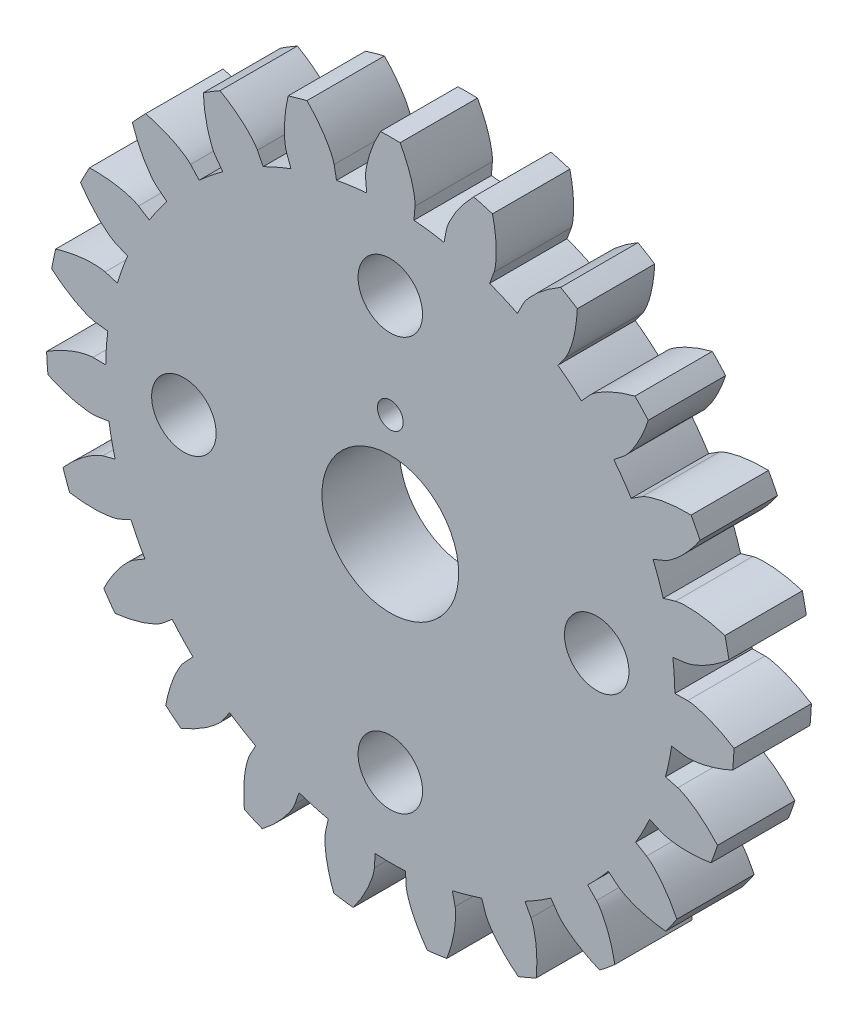
SolidWorks part; units mm, degrees
ref_plane "Front Plane" through (0, 0, 0) normal (0, 0, 1) x (1, 0, 0)
ref_plane "Top Plane" through (0, 0, 0) normal (0, 1, 0) x (1, 0, 0)
ref_plane "Right Plane" through (0, 0, 0) normal (1, 0, 0) x (0, 0, -1)
sketch "Model" plane through (0, 0, 0) normal (0, 0, 1) x (1, 0, 0)
  line L0 (-3.5387, -10.448) -> (-3.6973, -10.9162)
  line L1 (-5.4543, -10.153) -> (-5.2204, -9.7176)
  line L2 (-6.2264, -9.1058) -> (-6.5054, -9.5139)
  line L3 (-7.9913, -8.3049) -> (-7.6486, -7.9488)
  line L4 (-8.4522, -7.0883) -> (-8.8309, -7.4059)
  line L5 (-9.9356, -5.8409) -> (-9.5095, -5.5904)
  line L6 (-10.0512, -4.5451) -> (-10.5016, -4.7487)
  line L7 (-11.1431, -2.9437) -> (-10.6651, -2.8175)
  line L8 (-10.9047, -1.6648) -> (-11.3933, -1.7394)
  line L9 (-11.524, 0.1718) -> (-11.0298, 0.1644)
  line L10 (-10.9495, 1.339) -> (-11.4401, 1.399)
  line L11 (-11.0504, 3.2746) -> (-10.5764, 3.1341)
  line L12 (-10.1822, 4.2435) -> (-10.6384, 4.4336)
  line L13 (-9.7571, 6.1345) -> (-9.3387, 5.8714)
  line L14 (-8.6597, 6.8332) -> (-9.0477, 7.1394)
  line L15 (-7.7402, 8.5394) -> (-7.4083, 8.1732)
  line L16 (-6.495, 8.9162) -> (-6.786, 9.3157)
  line L17 (-5.1493, 10.3111) -> (-4.9285, 9.8688)
  line L18 (-3.8486, 10.3379) -> (-4.021, 10.8011)
  line L19 (-2.1765, 11.318) -> (-2.0831, 10.8326)
  line L20 (-0.9167, 10.9929) -> (-0.9578, 11.4855)
  line L21 (0.9578, 11.4855) -> (0.9167, 10.9929)
  line L22 (2.0831, 10.8326) -> (2.1765, 11.318)
  line L23 (4.021, 10.8011) -> (3.8486, 10.3379)
  line L24 (4.9285, 9.8688) -> (5.1493, 10.3111)
  line L25 (6.786, 9.3157) -> (6.495, 8.9162)
  line L26 (7.4083, 8.1732) -> (7.7402, 8.5394)
  line L27 (9.0477, 7.1394) -> (8.6597, 6.8332)
  line L28 (9.3387, 5.8714) -> (9.7571, 6.1345)
  line L29 (10.6384, 4.4336) -> (10.1822, 4.2435)
  line L30 (10.5764, 3.1341) -> (11.0504, 3.2746)
  line L31 (11.4401, 1.399) -> (10.9495, 1.339)
  line L32 (11.0298, 0.1644) -> (11.524, 0.1718)
  line L33 (11.3933, -1.7394) -> (10.9047, -1.6648)
  line L34 (10.6651, -2.8175) -> (11.1431, -2.9437)
  line L35 (10.5016, -4.7487) -> (10.0512, -4.5451)
  line L36 (9.5095, -5.5904) -> (9.9356, -5.8409)
  line L37 (8.8309, -7.4059) -> (8.4522, -7.0883)
  line L38 (7.6486, -7.9488) -> (7.9913, -8.3049)
  line L39 (6.5054, -9.5139) -> (6.2264, -9.1058)
  line L40 (5.2204, -9.7176) -> (5.4543, -10.153)
  line L41 (3.6973, -10.9162) -> (3.5387, -10.448)
  line L42 (2.405, -10.7657) -> (2.5128, -11.2481)
  line L43 (0.6151, -11.5089) -> (0.5887, -11.0153)
  line L44 (-0.5887, -11.0153) -> (-0.6151, -11.5089)
  line L45 (-2.5128, -11.2481) -> (-2.405, -10.7657)
  arc A0 (-5.6568, -12.0719) -> (-4.9615, -12.3739) centre (0, 0) ccw
  arc A1 (-6.2264, -9.1058) -> (-5.2204, -9.7176) centre (0, 0) ccw
  arc A2 (-8.704, -10.098) -> (-8.1159, -10.5765) centre (0, 0) ccw
  arc A3 (-8.4522, -7.0883) -> (-7.6486, -7.9488) centre (0, 0) ccw
  arc A4 (-11.1057, -7.3752) -> (-10.6684, -7.9946) centre (0, 0) ccw
  arc A5 (-10.0512, -4.5451) -> (-9.5095, -5.5904) centre (0, 0) ccw
  arc A6 (-12.6836, -4.1055) -> (-12.4297, -4.8198) centre (0, 0) ccw
  arc A7 (-10.9047, -1.6648) -> (-10.6651, -2.8175) centre (0, 0) ccw
  arc A8 (-13.3209, -0.5312) -> (-13.2692, -1.2876) centre (0, 0) ccw
  arc A9 (-10.9495, 1.339) -> (-11.0298, 0.1644) centre (0, 0) ccw
  arc A10 (-12.9703, 3.0824) -> (-13.1245, 2.3401) centre (0, 0) ccw
  arc A11 (-10.1822, 4.2435) -> (-10.5764, 3.1341) centre (0, 0) ccw
  arc A12 (-11.6577, 6.4675) -> (-12.0065, 5.7943) centre (0, 0) ccw
  arc A13 (-8.6597, 6.8332) -> (-9.3387, 5.8714) centre (0, 0) ccw
  arc A14 (-9.4805, 9.3728) -> (-9.998, 8.8187) centre (0, 0) ccw
  arc A15 (-6.495, 8.9162) -> (-7.4083, 8.1732) centre (0, 0) ccw
  arc A16 (-6.6002, 11.5831) -> (-7.2479, 11.1891) centre (0, 0) ccw
  arc A17 (-3.8486, 10.3379) -> (-4.9285, 9.8688) centre (0, 0) ccw
  arc A18 (-3.2303, 12.9342) -> (-3.9604, 12.7297) centre (0, 0) ccw
  arc A19 (-0.9167, 10.9929) -> (-2.0831, 10.8326) centre (0, 0) ccw
  arc A20 (0.3791, 13.3261) -> (-0.3791, 13.3261) centre (0, 0) ccw
  arc A21 (2.0831, 10.8326) -> (0.9167, 10.9929) centre (0, 0) ccw
  arc A22 (3.9604, 12.7297) -> (3.2303, 12.9342) centre (0, 0) ccw
  arc A23 (4.9285, 9.8688) -> (3.8486, 10.3379) centre (0, 0) ccw
  arc A24 (7.2479, 11.1891) -> (6.6002, 11.5831) centre (0, 0) ccw
  arc A25 (7.4083, 8.1732) -> (6.495, 8.9162) centre (0, 0) ccw
  arc A26 (9.998, 8.8187) -> (9.4805, 9.3728) centre (0, 0) ccw
  arc A27 (9.3387, 5.8714) -> (8.6597, 6.8332) centre (0, 0) ccw
  arc A28 (12.0065, 5.7943) -> (11.6577, 6.4675) centre (0, 0) ccw
  arc A29 (10.5764, 3.1341) -> (10.1822, 4.2435) centre (0, 0) ccw
  arc A30 (13.1245, 2.3401) -> (12.9703, 3.0824) centre (0, 0) ccw
  arc A31 (11.0298, 0.1644) -> (10.9495, 1.339) centre (0, 0) ccw
  arc A32 (13.2692, -1.2876) -> (13.3209, -0.5312) centre (0, 0) ccw
  arc A33 (10.6651, -2.8175) -> (10.9047, -1.6648) centre (0, 0) ccw
  arc A34 (12.4297, -4.8198) -> (12.6836, -4.1055) centre (0, 0) ccw
  arc A35 (9.5095, -5.5904) -> (10.0512, -4.5451) centre (0, 0) ccw
  arc A36 (10.6684, -7.9946) -> (11.1057, -7.3752) centre (0, 0) ccw
  arc A37 (7.6486, -7.9488) -> (8.4522, -7.0883) centre (0, 0) ccw
  arc A38 (8.1159, -10.5765) -> (8.704, -10.098) centre (0, 0) ccw
  arc A39 (5.2204, -9.7176) -> (6.2264, -9.1058) centre (0, 0) ccw
  arc A40 (4.9615, -12.3739) -> (5.6568, -12.0719) centre (0, 0) ccw
  arc A41 (2.405, -10.7657) -> (3.5387, -10.448) centre (0, 0) ccw
  arc A42 (1.439, -13.2536) -> (2.1901, -13.1504) centre (0, 0) ccw
  arc A43 (-0.5887, -11.0153) -> (0.5887, -11.0153) centre (0, 0) ccw
  arc A44 (-2.1901, -13.1504) -> (-1.439, -13.2536) centre (0, 0) ccw
  arc A45 (-3.5387, -10.448) -> (-2.405, -10.7657) centre (0, 0) ccw
  circle A46 centre (0, 0) radius 12.265 construction
  spline S0 degree 3 poles (-3.6973, -10.9162) (-3.7069, -10.9403) (-3.7475, -11.036) (-3.8652, -11.2386) (-4.0935, -11.5548) (-4.4634, -11.9567) (-4.7761, -12.2317) (-4.9615, -12.3739) knots 34.584629 34.584629 34.584629 34.584629 34.662509 34.896108 35.285436 35.830493 36.531279 36.531279 36.531279 36.531279
  spline S1 degree 3 poles (-5.6568, -12.0719) (-5.6795, -11.8394) (-5.6919, -11.4231) (-5.6506, -10.8784) (-5.5754, -10.4958) (-5.5076, -10.2714) (-5.4654, -10.1765) (-5.4543, -10.153) knots 37.289537 37.289537 37.289537 37.289537 37.990323 38.535379 38.924707 39.158307 39.236186 39.236186 39.236186 39.236186
  spline S2 degree 3 poles (-6.5054, -9.5139) (-6.5211, -9.5345) (-6.586, -9.6157) (-6.754, -9.779) (-7.0591, -10.0219) (-7.5237, -10.3091) (-7.8991, -10.4896) (-8.1159, -10.5765) knots 41.402696 41.402696 41.402696 41.402696 41.480575 41.714175 42.103503 42.648559 43.349345 43.349345 43.349345 43.349345
  spline S3 degree 3 poles (-8.704, -10.098) (-8.6631, -9.868) (-8.5627, -9.4638) (-8.376, -8.9505) (-8.2003, -8.6023) (-8.0746, -8.4046) (-8.0083, -8.3246) (-7.9913, -8.3049) knots 44.107603 44.107603 44.107603 44.107603 44.808389 45.353446 45.742774 45.976373 46.054253 46.054253 46.054253 46.054253
  spline S4 degree 3 poles (-8.8309, -7.4059) (-8.8517, -7.4216) (-8.936, -7.4822) (-9.1419, -7.5942) (-9.5012, -7.7457) (-10.0261, -7.8969) (-10.4362, -7.9695) (-10.6684, -7.9946) knots 48.220763 48.220763 48.220763 48.220763 48.298642 48.532242 48.921569 49.466626 50.167412 50.167412 50.167412 50.167412
  spline S5 degree 3 poles (-11.1057, -7.3752) (-11.0042, -7.1648) (-10.7985, -6.8027) (-10.4802, -6.3587) (-10.2171, -6.0709) (-10.0427, -5.9144) (-9.9573, -5.8552) (-9.9356, -5.8409) knots 50.92567 50.92567 50.92567 50.92567 51.626456 52.171513 52.56084 52.79444 52.87232 52.87232 52.87232 52.87232
  spline S6 degree 3 poles (-10.5016, -4.7487) (-10.5257, -4.7582) (-10.6233, -4.7938) (-10.8518, -4.8461) (-11.2386, -4.8951) (-11.7849, -4.8991) (-12.1993, -4.8583) (-12.4297, -4.8198) knots 55.038829 55.038829 55.038829 55.038829 55.116709 55.350309 55.739636 56.284693 56.985479 56.985479 56.985479 56.985479
  spline S7 degree 3 poles (-12.6836, -4.1055) (-12.5292, -3.9302) (-12.2334, -3.637) (-11.8072, -3.2954) (-11.4762, -3.0892) (-11.266, -2.9856) (-11.1678, -2.9517) (-11.1431, -2.9437) knots 57.743737 57.743737 57.743737 57.743737 58.444523 58.98958 59.378907 59.612507 59.690386 59.690386 59.690386 59.690386
  spline S8 degree 3 poles (-11.3933, -1.7394) (-11.4192, -1.7419) (-11.5228, -1.7499) (-11.7568, -1.7386) (-12.1426, -1.6814) (-12.6696, -1.5379) (-13.0577, -1.3868) (-13.2692, -1.2876) knots 61.856896 61.856896 61.856896 61.856896 61.934776 62.168375 62.557703 63.102759 63.803546 63.803546 63.803546 63.803546
  spline S9 degree 3 poles (-13.3209, -0.5312) (-13.1249, -0.4042) (-12.761, -0.2016) (-12.2584, 0.0123) (-11.8841, 0.1216) (-11.6537, 0.1646) (-11.55, 0.1708) (-11.524, 0.1718) knots 64.561804 64.561804 64.561804 64.561804 65.26259 65.807646 66.196974 66.430574 66.508453 66.508453 66.508453 66.508453
  spline S10 degree 3 poles (-11.4401, 1.399) (-11.4657, 1.4035) (-11.5676, 1.4238) (-11.7899, 1.4978) (-12.1459, 1.657) (-12.6147, 1.9374) (-12.9476, 2.1876) (-13.1245, 2.3401) knots 68.674963 68.674963 68.674963 68.674963 68.752842 68.986442 69.37577 69.920826 70.621612 70.621612 70.621612 70.621612
  spline S11 degree 3 poles (-12.9703, 3.0824) (-12.7472, 3.1519) (-12.3422, 3.2487) (-11.8005, 3.3192) (-11.4106, 3.3233) (-11.1772, 3.3026) (-11.0756, 3.2806) (-11.0504, 3.2746) knots 71.37987 71.37987 71.37987 71.37987 72.080656 72.625713 73.015041 73.24864 73.32652 73.32652 73.32652 73.32652
  spline S12 degree 3 poles (-10.6384, 4.4336) (-10.6618, 4.4449) (-10.7545, 4.4919) (-10.9486, 4.6231) (-11.2485, 4.8724) (-11.6242, 5.2689) (-11.8773, 5.5997) (-12.0065, 5.7943) knots 75.493029 75.493029 75.493029 75.493029 75.570909 75.804509 76.193836 76.738893 77.439679 77.439679 77.439679 77.439679
  spline S13 degree 3 poles (-11.6577, 6.4675) (-11.4242, 6.4742) (-11.008, 6.4581) (-10.4674, 6.3798) (-10.0908, 6.2786) (-9.8716, 6.1957) (-9.7798, 6.1471) (-9.7571, 6.1345) knots 78.197937 78.197937 78.197937 78.197937 78.898723 79.44378 79.833107 80.066707 80.144586 80.144586 80.144586 80.144586
  spline S14 degree 3 poles (-9.0477, 7.1394) (-9.0673, 7.1566) (-9.1438, 7.2268) (-9.2953, 7.4056) (-9.5168, 7.7266) (-9.7716, 8.2097) (-9.9261, 8.5965) (-9.998, 8.8187) knots 82.311096 82.311096 82.311096 82.311096 82.388976 82.622575 83.011903 83.55696 84.257746 84.257746 84.257746 84.257746
  spline S15 degree 3 poles (-9.4805, 9.3728) (-9.2538, 9.3163) (-8.8574, 9.1886) (-8.358, 8.9673) (-8.0227, 8.7683) (-7.834, 8.6293) (-7.7586, 8.5577) (-7.7402, 8.5394) knots 85.016004 85.016004 85.016004 85.016004 85.71679 86.261846 86.651174 86.884774 86.962653 86.962653 86.962653 86.962653
  spline S16 degree 3 poles (-6.786, 9.3157) (-6.8002, 9.3375) (-6.8549, 9.4258) (-6.9526, 9.6388) (-7.0793, 10.0076) (-7.1943, 10.5416) (-7.2387, 10.9557) (-7.2479, 11.1891) knots 89.129163 89.129163 89.129163 89.129163 89.207042 89.440642 89.82997 90.375026 91.075812 91.075812 91.075812 91.075812
  spline S17 degree 3 poles (-6.6002, 11.5831) (-6.3972, 11.4675) (-6.0499, 11.2375) (-5.6287, 10.8897) (-5.3595, 10.6076) (-5.2153, 10.4229) (-5.1621, 10.3337) (-5.1493, 10.3111) knots 91.83407 91.83407 91.83407 91.83407 92.534856 93.079913 93.469241 93.70284 93.78072 93.78072 93.78072 93.78072
  spline S18 degree 3 poles (-4.021, 10.8011) (-4.0288, 10.8259) (-4.0577, 10.9257) (-4.0943, 11.1572) (-4.1167, 11.5465) (-4.0834, 12.0917) (-4.0144, 12.5024) (-3.9604, 12.7297) knots 95.947229 95.947229 95.947229 95.947229 96.025109 96.258709 96.648036 97.193093 97.893879 97.893879 97.893879 97.893879
  spline S19 degree 3 poles (-3.2303, 12.9342) (-3.0661, 12.7682) (-2.7937, 12.4531) (-2.482, 12.0045) (-2.2989, 11.6602) (-2.2099, 11.4435) (-2.1827, 11.3432) (-2.1765, 11.318) knots 98.652137 98.652137 98.652137 98.652137 99.352923 99.89798 100.287307 100.520907 100.598787 100.598787 100.598787 100.598787
  spline S20 degree 3 poles (-0.9578, 11.4855) (-0.9586, 11.5114) (-0.9595, 11.6153) (-0.9323, 11.8481) (-0.8489, 12.229) (-0.6697, 12.745) (-0.4925, 13.1219) (-0.3791, 13.3261) knots 102.765296 102.765296 102.765296 102.765296 102.843176 103.076775 103.466103 104.01116 104.711946 104.711946 104.711946 104.711946
  spline S21 degree 3 poles (0.3791, 13.3261) (0.4925, 13.1219) (0.6697, 12.745) (0.8489, 12.229) (0.9323, 11.8481) (0.9595, 11.6153) (0.9586, 11.5114) (0.9578, 11.4855) knots 105.470204 105.470204 105.470204 105.470204 106.17099 106.716046 107.105374 107.338974 107.416853 107.416853 107.416853 107.416853
  spline S22 degree 3 poles (2.1765, 11.318) (2.1827, 11.3432) (2.2099, 11.4435) (2.2989, 11.6602) (2.482, 12.0045) (2.7937, 12.4531) (3.0661, 12.7682) (3.2303, 12.9342) knots 109.583363 109.583363 109.583363 109.583363 109.661242 109.894842 110.28417 110.829226 111.530012 111.530012 111.530012 111.530012
  spline S23 degree 3 poles (3.9604, 12.7297) (4.0144, 12.5024) (4.0834, 12.0917) (4.1167, 11.5465) (4.0943, 11.1572) (4.0577, 10.9257) (4.0288, 10.8259) (4.021, 10.8011) knots 112.28827 112.28827 112.28827 112.28827 112.989057 113.534113 113.923441 114.15704 114.23492 114.23492 114.23492 114.23492
  spline S24 degree 3 poles (5.1493, 10.3111) (5.1621, 10.3337) (5.2153, 10.4229) (5.3595, 10.6076) (5.6287, 10.8897) (6.0499, 11.2375) (6.3972, 11.4675) (6.6002, 11.5831) knots 116.40143 116.40143 116.40143 116.40143 116.479309 116.712909 117.102236 117.647293 118.348079 118.348079 118.348079 118.348079
  spline S25 degree 3 poles (7.2479, 11.1891) (7.2387, 10.9557) (7.1943, 10.5416) (7.0793, 10.0076) (6.9526, 9.6388) (6.8549, 9.4258) (6.8002, 9.3375) (6.786, 9.3157) knots 119.106337 119.106337 119.106337 119.106337 119.807123 120.35218 120.741507 120.975107 121.052987 121.052987 121.052987 121.052987
  spline S26 degree 3 poles (7.7402, 8.5394) (7.7586, 8.5577) (7.834, 8.6293) (8.0227, 8.7683) (8.358, 8.9673) (8.8574, 9.1886) (9.2538, 9.3163) (9.4805, 9.3728) knots 123.219496 123.219496 123.219496 123.219496 123.297376 123.530976 123.920303 124.46536 125.166146 125.166146 125.166146 125.166146
  spline S27 degree 3 poles (9.998, 8.8187) (9.9261, 8.5965) (9.7716, 8.2097) (9.5168, 7.7266) (9.2953, 7.4056) (9.1438, 7.2268) (9.0673, 7.1566) (9.0477, 7.1394) knots 125.924404 125.924404 125.924404 125.924404 126.62519 127.170247 127.559574 127.793174 127.871053 127.871053 127.871053 127.871053
  spline S28 degree 3 poles (9.7571, 6.1345) (9.7798, 6.1471) (9.8716, 6.1957) (10.0908, 6.2786) (10.4674, 6.3798) (11.008, 6.4581) (11.4242, 6.4742) (11.6577, 6.4675) knots 130.037563 130.037563 130.037563 130.037563 130.115443 130.349042 130.73837 131.283426 131.984213 131.984213 131.984213 131.984213
  spline S29 degree 3 poles (12.0065, 5.7943) (11.8773, 5.5997) (11.6242, 5.2689) (11.2485, 4.8724) (10.9486, 4.6231) (10.7545, 4.4919) (10.6618, 4.4449) (10.6384, 4.4336) knots 132.742471 132.742471 132.742471 132.742471 133.443257 133.988313 134.377641 134.611241 134.68912 134.68912 134.68912 134.68912
  spline S30 degree 3 poles (11.0504, 3.2746) (11.0756, 3.2806) (11.1772, 3.3026) (11.4106, 3.3233) (11.8005, 3.3192) (12.3422, 3.2487) (12.7472, 3.1519) (12.9703, 3.0824) knots 136.85563 136.85563 136.85563 136.85563 136.933509 137.167109 137.556437 138.101493 138.802279 138.802279 138.802279 138.802279
  spline S31 degree 3 poles (13.1245, 2.3401) (12.9476, 2.1876) (12.6147, 1.9374) (12.1459, 1.657) (11.7899, 1.4978) (11.5676, 1.4238) (11.4657, 1.4035) (11.4401, 1.399) knots 139.560537 139.560537 139.560537 139.560537 140.261323 140.80638 141.195708 141.429307 141.507187 141.507187 141.507187 141.507187
  spline S32 degree 3 poles (11.524, 0.1718) (11.55, 0.1708) (11.6537, 0.1646) (11.8841, 0.1216) (12.2584, 0.0123) (12.761, -0.2016) (13.1249, -0.4042) (13.3209, -0.5312) knots 143.673696 143.673696 143.673696 143.673696 143.751576 143.985176 144.374503 144.91956 145.620346 145.620346 145.620346 145.620346
  spline S33 degree 3 poles (13.2692, -1.2876) (13.0577, -1.3868) (12.6696, -1.5379) (12.1426, -1.6814) (11.7568, -1.7386) (11.5228, -1.7499) (11.4192, -1.7419) (11.3933, -1.7394) knots 146.378604 146.378604 146.378604 146.378604 147.07939 147.624447 148.013774 148.247374 148.325254 148.325254 148.325254 148.325254
  spline S34 degree 3 poles (11.1431, -2.9437) (11.1678, -2.9517) (11.266, -2.9856) (11.4762, -3.0892) (11.8072, -3.2954) (12.2334, -3.637) (12.5292, -3.9302) (12.6836, -4.1055) knots 150.491763 150.491763 150.491763 150.491763 150.569643 150.803242 151.19257 151.737627 152.438413 152.438413 152.438413 152.438413
  spline S35 degree 3 poles (12.4297, -4.8198) (12.1993, -4.8583) (11.7849, -4.8991) (11.2386, -4.8951) (10.8518, -4.8461) (10.6233, -4.7938) (10.5257, -4.7582) (10.5016, -4.7487) knots 153.196671 153.196671 153.196671 153.196671 153.897457 154.442513 154.831841 155.065441 155.14332 155.14332 155.14332 155.14332
  spline S36 degree 3 poles (9.9356, -5.8409) (9.9573, -5.8552) (10.0427, -5.9144) (10.2171, -6.0709) (10.4802, -6.3587) (10.7985, -6.8027) (11.0042, -7.1648) (11.1057, -7.3752) knots 157.30983 157.30983 157.30983 157.30983 157.387709 157.621309 158.010637 158.555693 159.256479 159.256479 159.256479 159.256479
  spline S37 degree 3 poles (10.6684, -7.9946) (10.4362, -7.9695) (10.0261, -7.8969) (9.5012, -7.7457) (9.1419, -7.5942) (8.936, -7.4822) (8.8517, -7.4216) (8.8309, -7.4059) knots 160.014737 160.014737 160.014737 160.014737 160.715523 161.26058 161.649908 161.883507 161.961387 161.961387 161.961387 161.961387
  spline S38 degree 3 poles (7.9913, -8.3049) (8.0083, -8.3246) (8.0746, -8.4046) (8.2003, -8.6023) (8.376, -8.9505) (8.5627, -9.4638) (8.6631, -9.868) (8.704, -10.098) knots 164.127897 164.127897 164.127897 164.127897 164.205776 164.439376 164.828703 165.37376 166.074546 166.074546 166.074546 166.074546
  spline S39 degree 3 poles (8.1159, -10.5765) (7.8991, -10.4896) (7.5237, -10.3091) (7.0591, -10.0219) (6.754, -9.779) (6.586, -9.6157) (6.5211, -9.5345) (6.5054, -9.5139) knots 166.832804 166.832804 166.832804 166.832804 167.53359 168.078647 168.467974 168.701574 168.779454 168.779454 168.779454 168.779454
  spline S40 degree 3 poles (5.4543, -10.153) (5.4654, -10.1765) (5.5076, -10.2714) (5.5754, -10.4958) (5.6506, -10.8784) (5.6919, -11.4231) (5.6795, -11.8394) (5.6568, -12.0719) knots 170.945963 170.945963 170.945963 170.945963 171.023843 171.257442 171.64677 172.191827 172.892613 172.892613 172.892613 172.892613
  spline S41 degree 3 poles (4.9615, -12.3739) (4.7761, -12.2317) (4.4634, -11.9567) (4.0935, -11.5548) (3.8652, -11.2386) (3.7475, -11.036) (3.7069, -10.9403) (3.6973, -10.9162) knots 173.650871 173.650871 173.650871 173.650871 174.351657 174.896713 175.286041 175.519641 175.59752 175.59752 175.59752 175.59752
  spline S42 degree 3 poles (2.5128, -11.2481) (2.5172, -11.2737) (2.5322, -11.3765) (2.5369, -11.6108) (2.5061, -11.9995) (2.3989, -12.5351) (2.2746, -12.9326) (2.1901, -13.1504) knots 177.76403 177.76403 177.76403 177.76403 177.841909 178.075509 178.464837 179.009893 179.710679 179.710679 179.710679 179.710679
  spline S43 degree 3 poles (1.439, -13.2536) (1.2989, -13.0667) (1.072, -12.7175) (0.8242, -12.2307) (0.6897, -11.8647) (0.6311, -11.6378) (0.6178, -11.5347) (0.6151, -11.5089) knots 180.468937 180.468937 180.468937 180.468937 181.169724 181.71478 182.104108 182.337707 182.415587 182.415587 182.415587 182.415587
  spline S44 degree 3 poles (-0.6151, -11.5089) (-0.6178, -11.5347) (-0.6311, -11.6378) (-0.6897, -11.8647) (-0.8242, -12.2307) (-1.072, -12.7175) (-1.2989, -13.0667) (-1.439, -13.2536) knots 184.582097 184.582097 184.582097 184.582097 184.659976 184.893576 185.282903 185.82796 186.528746 186.528746 186.528746 186.528746
  spline S45 degree 3 poles (-2.1901, -13.1504) (-2.2746, -12.9326) (-2.3989, -12.5351) (-2.5061, -11.9995) (-2.5369, -11.6108) (-2.5322, -11.3765) (-2.5172, -11.2737) (-2.5128, -11.2481) knots 187.287004 187.287004 187.287004 187.287004 187.98779 188.532847 188.922174 189.155774 189.233654 189.233654 189.233654 189.233654
extrude "Boss-Extrude1" add sketch "Model" along normal blind 3
sketch "Sketch2" plane through (0, 0, 0) normal (0, 0, 1) x (1, 0, 0)
  line L0 (0, 8) -> (0, 0) construction
  circle A0 centre (0, 0) radius 2.65
  circle A1 centre (0, 0) radius 8 construction
  circle A2 centre (0, 8) radius 1.25
  circle A3 centre (-8, 0) radius 1.25
  circle A4 centre (0, -8) radius 1.25
  circle A5 centre (8, 0) radius 1.25
  circle A6 centre (0, 4) radius 0.5
  dimension "D1" = 5.3
  dimension "D2" = 16
  dimension "D3" = 2.5
  dimension "D4" = 1
extrude "Cut-Extrude1" cut sketch "Sketch2" along normal through all
sketch "Sketch3" plane through (0, 0, 3) normal (0, 0, 1) x (1, 0, 0)
  line L0 (0, 2.65) -> (0, 2.925)
  line L1 (0.659, 2.5667) -> (0.7274, 2.8331)
  line L2 (1.2766, 2.3222) -> (1.4091, 2.5632)
  line L3 (1.814, 1.9318) -> (2.0023, 2.1322)
  line L4 (2.2375, 1.4199) -> (2.4697, 1.5673)
  line L5 (2.5203, 0.8189) -> (2.7818, 0.9039)
  line L6 (2.6448, 0.1664) -> (2.9192, 0.1837)
  line L7 (2.6031, -0.4966) -> (2.8732, -0.5481)
  line L8 (2.3978, -1.1283) -> (2.6466, -1.2454)
  line L9 (2.0419, -1.6892) -> (2.2538, -1.8645)
  line L10 (1.5576, -2.1439) -> (1.7193, -2.3664)
  line L11 (0.9755, -2.4639) -> (1.0768, -2.7196)
  line L12 (0.3321, -2.6291) -> (0.3666, -2.9019)
  line L13 (-0.3321, -2.6291) -> (-0.3666, -2.9019)
  line L14 (-0.9755, -2.4639) -> (-1.0768, -2.7196)
  line L15 (-1.5576, -2.1439) -> (-1.7193, -2.3664)
  line L16 (-2.0419, -1.6892) -> (-2.2538, -1.8645)
  line L17 (-2.3978, -1.1283) -> (-2.6466, -1.2454)
  line L18 (-2.6031, -0.4966) -> (-2.8732, -0.5481)
  line L19 (-2.6448, 0.1664) -> (-2.9192, 0.1837)
  line L20 (-2.5203, 0.8189) -> (-2.7818, 0.9039)
  line L21 (-2.2375, 1.4199) -> (-2.4697, 1.5673)
  line L22 (-1.814, 1.9318) -> (-2.0023, 2.1322)
  line L23 (-1.2766, 2.3222) -> (-1.4091, 2.5632)
  line L24 (-0.659, 2.5667) -> (-0.7274, 2.8331)
  circle A0 centre (0, 0) radius 2.65 construction
  point P4 (0, 0)
  point P57 (0, 0)
  dimension "D1" = 0.275
  dimension "D2" = 25
